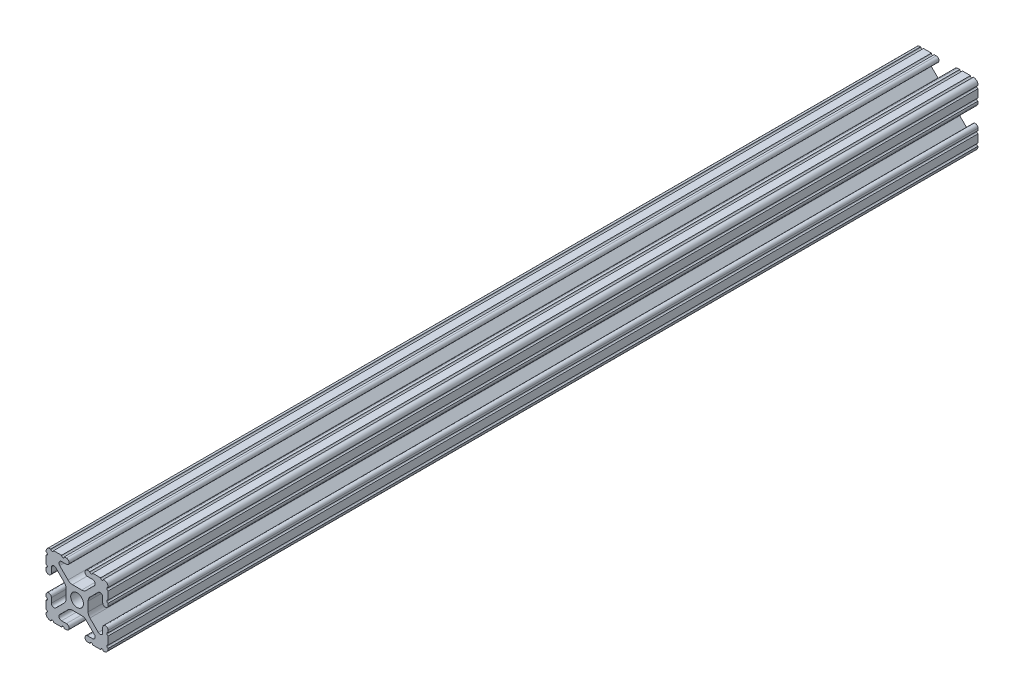
SolidWorks part; units mm, degrees
ref_plane "Front Plane" through (0, 0, 0) normal (0, 0, 1) x (1, 0, 0)
ref_plane "Top Plane" through (0, 0, 0) normal (0, 1, 0) x (1, 0, 0)
ref_plane "Right Plane" through (0, 0, 0) normal (1, 0, 0) x (0, 0, -1)
sketch "Sketch1" plane through (0, 0, 0) normal (0, 0, 1) x (1, 0, 0)
  line L0 (0, -12.7) -> (0, 12.7) construction
  line L1 (12.7, 0) -> (-12.7, 0) construction
  line L2 (3.2512, 12.7) -> (-3.2512, 12.7) construction
  line L3 (0, -4.5212) -> (0, 4.5212) construction
  line L4 (-3.2512, 12.7) -> (-3.2512, 10.4902) construction
  line L5 (12.7, -7.4168) -> (12.7, 7.4168) construction
  line L6 (0, -2.6035) -> (0, 2.6035) construction
  point P4 (0, 0)
  point P8 (0, 0)
  point P11 (0, 12.7)
  point P14 (0, 0)
  point P18 (12.7, 0)
  point P21 (0, 0)
sketch "Sketch2" plane through (0, 0, 0) normal (1, 0, 0) x (0, 0, -1)
  line L0 (-177.8, 0) -> (177.8, 0) construction
  point P4 (0, 0)
  dimension "Length" = 355.6
sketch "Sketch3" plane through (0, 0, 0) normal (0, 0, 1) x (1, 0, 0)
  line L1 (12.7, -12.7) -> (-12.7, -12.7)
  line L2 (12.7, -12.7) -> (12.7, 12.7)
  line L3 (12.7, 12.7) -> (-12.7, 12.7)
  line L4 (-12.7, -12.7) -> (-12.7, 12.7)
  line L5 (12.7, -12.7) -> (-12.7, 12.7) construction
  line L6 (12.7, 12.7) -> (-12.7, -12.7) construction
  point P0 (0, 0)
extrude "Boss-Extrude1" add sketch "Sketch3" along normal up to vertex (177.8 mm away) and the other way up to vertex (177.8 mm away) up to point (0, 0, 177.8) other way up to point (0, 0, -177.8)
sketch "Sketch4" plane through (0, 0, 177.8) normal (0, 0, 1) x (1, 0, 0)
  line L0 (-3.2512, 12.7) -> (-3.2512, 10.4902)
  line L1 (-3.2512, 10.4902) -> (-8.9276, 10.4902)
  line L2 (-8.9276, 10.4902) -> (-2.9586, 4.5212)
  line L3 (-2.9586, 4.5212) -> (2.9586, 4.5212)
  line L4 (0, -12.7) -> (0, 12.7) construction
  line L5 (12.7, 12.7) -> (-12.7, 12.7) construction
  line L6 (0, 12.7) -> (0, -12.7) construction
  line L7 (-12.7, 0) -> (12.7, 0) construction
  line L8 (-12.7, 12.7) -> (0, 0) construction
  line L9 (-12.7, 3.2512) -> (-10.4902, 3.2512)
  line L10 (-10.4902, 3.2512) -> (-10.4902, 8.9276)
  line L11 (-10.4902, 8.9276) -> (-4.5212, 2.9586)
  line L12 (-4.5212, 2.9586) -> (-4.5212, -2.9586)
  line L13 (4.5212, 2.9586) -> (4.5212, -2.9586)
  line L14 (10.4902, 8.9276) -> (4.5212, 2.9586)
  line L15 (10.4902, 3.2512) -> (10.4902, 8.9276)
  line L16 (12.7, 3.2512) -> (10.4902, 3.2512)
  line L17 (8.9276, 10.4902) -> (2.9586, 4.5212)
  line L18 (3.2512, 10.4902) -> (8.9276, 10.4902)
  line L19 (3.2512, 12.7) -> (3.2512, 10.4902)
  line L20 (3.2512, -12.7) -> (3.2512, -10.4902)
  line L21 (3.2512, -10.4902) -> (8.9276, -10.4902)
  line L22 (8.9276, -10.4902) -> (2.9586, -4.5212)
  line L23 (12.7, -3.2512) -> (10.4902, -3.2512)
  line L24 (10.4902, -3.2512) -> (10.4902, -8.9276)
  line L25 (10.4902, -8.9276) -> (4.5212, -2.9586)
  line L26 (-10.4902, -8.9276) -> (-4.5212, -2.9586)
  line L27 (-10.4902, -3.2512) -> (-10.4902, -8.9276)
  line L28 (-12.7, -3.2512) -> (-10.4902, -3.2512)
  line L29 (-2.9586, -4.5212) -> (2.9586, -4.5212)
  line L30 (-8.9276, -10.4902) -> (-2.9586, -4.5212)
  line L31 (-3.2512, -10.4902) -> (-8.9276, -10.4902)
  line L32 (-3.2512, -12.7) -> (-3.2512, -10.4902)
  line L33 (-12.7, 3.2512) -> (-12.7, -3.2512)
  line L34 (-3.2512, -12.7) -> (3.2512, -12.7)
  line L35 (12.7, -3.2512) -> (12.7, 3.2512)
  line L36 (3.2512, 12.7) -> (-3.2512, 12.7)
  line L37 (-12.7, 12.7) -> (-12.7, -12.7) construction
  line L38 (-12.7, -12.7) -> (12.7, -12.7) construction
  arc A3 (-6.3485, 10.4902) -> (-7.1039, 8.6665) centre (-6.3485, 9.4219) ccw
  arc A4 (7.1039, 8.6665) -> (6.3485, 10.4902) centre (6.3485, 9.4219) ccw
  arc A5 (8.6665, -7.1039) -> (10.4902, -6.3485) centre (9.4219, -6.3485) ccw
  arc A6 (10.4902, 6.3485) -> (8.6665, 7.1039) centre (9.4219, 6.3485) ccw
  arc A7 (-7.1039, -8.6665) -> (-6.3485, -10.4902) centre (-6.3485, -9.4219) ccw
  arc A8 (6.3485, -10.4902) -> (7.1039, -8.6665) centre (6.3485, -9.4219) ccw
  arc A9 (-8.6665, 7.1039) -> (-10.4902, 6.3485) centre (-9.4219, 6.3485) ccw
  arc A10 (-10.4902, -6.3485) -> (-8.6665, -7.1039) centre (-9.4219, -6.3485) ccw
  circle A11 centre (0, 0) radius 2.6035
  point P34 (0, 4.5212)
  point P45 (4.5212, 0)
  point P46 (-4.5212, 0)
  point P53 (0, -4.5212)
  point P81 (0, 0)
  line M2 (-12.7, 12.7) -> (-12.7, -12.7)
  line M3 (-12.7, -12.7) -> (12.7, -12.7)
  line M4 (12.7, -12.7) -> (12.7, 12.7)
  line M5 (12.7, 12.7) -> (-12.7, 12.7)
  dimension "D5" = 5.207
  dimension "D1" = 2.2098
  dimension "D2" = 2.2098
  dimension "D3" = 14.8336
  dimension "D4" = 4
extrude "Cut-Extrude1" cut sketch "Sketch4" against normal through all contours L17 A4 L18 L19 L0 L1 A3 L2 L3 M5 | L15 A6 L14 L13 L25 A5 L24 L23 L16 M4 | L21 A8 L22 L29 L30 A7 L31 L32 L20 M3 | L27 A10 L26 L12 L11 A9 L10 L9 L28 M2 | A11
sketch "Sketch5" plane through (0, 0, 177.8) normal (0, 0, 1) x (1, 0, 0)
  line L0 (-4.3561, 12.7) -> (-3.2512, 12.7)
  line L1 (-3.2512, 12.7) -> (-3.2512, 10.4902)
  line L2 (-3.2512, 10.4902) -> (-4.3561, 10.4902)
  line L3 (0, -12.7) -> (0, 12.7) construction
  line L4 (-3.2512, 12.7) -> (-12.7, 12.7) construction
  line L5 (3.2512, 10.4902) -> (4.3561, 10.4902)
  line L6 (3.2512, 12.7) -> (3.2512, 10.4902)
  line L7 (4.3561, 12.7) -> (3.2512, 12.7)
  line L8 (12.7, 4.3561) -> (12.7, 3.2512)
  line L9 (12.7, 3.2512) -> (10.4902, 3.2512)
  line L10 (10.4902, 3.2512) -> (10.4902, 4.3561)
  line L11 (10.4902, -3.2512) -> (10.4902, -4.3561)
  line L12 (12.7, -3.2512) -> (10.4902, -3.2512)
  line L13 (12.7, -4.3561) -> (12.7, -3.2512)
  line L14 (4.3561, -12.7) -> (3.2512, -12.7)
  line L15 (3.2512, -12.7) -> (3.2512, -10.4902)
  line L16 (3.2512, -10.4902) -> (4.3561, -10.4902)
  line L17 (-3.2512, -10.4902) -> (-4.3561, -10.4902)
  line L18 (-3.2512, -12.7) -> (-3.2512, -10.4902)
  line L19 (-4.3561, -12.7) -> (-3.2512, -12.7)
  line L20 (-12.7, -4.3561) -> (-12.7, -3.2512)
  line L21 (-12.7, -3.2512) -> (-10.4902, -3.2512)
  line L22 (-10.4902, -3.2512) -> (-10.4902, -4.3561)
  line L23 (-10.4902, 3.2512) -> (-10.4902, 4.3561)
  line L24 (-12.7, 3.2512) -> (-10.4902, 3.2512)
  line L25 (-12.7, 4.3561) -> (-12.7, 3.2512)
  line L26 (-12.7, 12.7) -> (-12.7, 3.2512) construction
  line L27 (-10.7124, 12.7) -> (-9.6075, 12.7)
  line L28 (-6.3436, 12.7) -> (-5.2387, 12.7)
  line L29 (-12.7, 10.7124) -> (-12.7, 9.6075)
  line L30 (-12.7, 6.3436) -> (-12.7, 5.2387)
  line L31 (6.3437, 12.7) -> (5.2388, 12.7)
  line L32 (10.7125, 12.7) -> (9.6076, 12.7)
  line L33 (12.7, 10.7125) -> (12.7, 9.6075)
  line L34 (12.7, 6.3436) -> (12.7, 5.2387)
  line L35 (12.7, -6.3437) -> (12.7, -5.2388)
  line L36 (12.7, -10.7125) -> (12.7, -9.6076)
  line L37 (10.7125, -12.7) -> (9.6076, -12.7)
  line L38 (6.3437, -12.7) -> (5.2388, -12.7)
  line L39 (-6.3436, -12.7) -> (-5.2387, -12.7)
  line L40 (-10.7124, -12.7) -> (-9.6075, -12.7)
  line L41 (-12.7, -10.7125) -> (-12.7, -9.6076)
  line L42 (-12.7, -6.3437) -> (-12.7, -5.2388)
  line L43 (12.7, 12.7) -> (3.2512, 12.7) construction
  line L44 (12.7, 3.2512) -> (12.7, 12.7) construction
  arc A0 (-4.3561, 10.4902) -> (-4.3561, 12.7) centre (-4.3561, 11.5951) ccw
  arc A1 (4.3561, 10.4902) -> (4.3561, 12.7) centre (4.3561, 11.5951) cw
  arc A2 (10.4902, 4.3561) -> (12.7, 4.3561) centre (11.5951, 4.3561) ccw
  arc A3 (10.4902, -4.3561) -> (12.7, -4.3561) centre (11.5951, -4.3561) cw
  arc A4 (4.3561, -10.4902) -> (4.3561, -12.7) centre (4.3561, -11.5951) ccw
  arc A5 (-4.3561, -10.4902) -> (-4.3561, -12.7) centre (-4.3561, -11.5951) cw
  arc A6 (-10.4902, -4.3561) -> (-12.7, -4.3561) centre (-11.5951, -4.3561) ccw
  arc A7 (-10.4902, 4.3561) -> (-12.7, 4.3561) centre (-11.5951, 4.3561) cw
  arc A8 (-10.7124, 12.7) -> (-9.6075, 12.7) centre (-10.16, 12.7) ccw
  arc A9 (-6.3436, 12.7) -> (-5.2387, 12.7) centre (-5.7912, 12.7) ccw
  arc A10 (-12.7, 9.6075) -> (-12.7, 10.7124) centre (-12.7, 10.16) ccw
  arc A11 (-12.7, 5.2387) -> (-12.7, 6.3436) centre (-12.7, 5.7912) ccw
  arc A12 (5.2388, 12.7) -> (6.3437, 12.7) centre (5.7912, 12.7) ccw
  arc A13 (9.6076, 12.7) -> (10.7125, 12.7) centre (10.16, 12.7) ccw
  arc A14 (12.7, 10.7125) -> (12.7, 9.6075) centre (12.7, 10.16) ccw
  arc A15 (12.7, 6.3436) -> (12.7, 5.2387) centre (12.7, 5.7912) ccw
  arc A16 (12.7, -5.2388) -> (12.7, -6.3437) centre (12.7, -5.7912) ccw
  arc A17 (12.7, -9.6076) -> (12.7, -10.7125) centre (12.7, -10.16) ccw
  arc A18 (10.7125, -12.7) -> (9.6076, -12.7) centre (10.16, -12.7) ccw
  arc A19 (6.3437, -12.7) -> (5.2388, -12.7) centre (5.7912, -12.7) ccw
  arc A20 (-5.2387, -12.7) -> (-6.3436, -12.7) centre (-5.7912, -12.7) ccw
  arc A21 (-9.6075, -12.7) -> (-10.7124, -12.7) centre (-10.16, -12.7) ccw
  arc A22 (-12.7, -10.7125) -> (-12.7, -9.6076) centre (-12.7, -10.16) ccw
  arc A23 (-12.7, -6.3437) -> (-12.7, -5.2388) centre (-12.7, -5.7912) ccw
  point P11 (0, 0)
  point P52 (0, 0)
  point P104 (0, 0)
  line M5 (3.2512, -10.4902) -> (3.2512, -12.7)
  line M6 (3.2512, -12.7) -> (12.7, -12.7)
  line M7 (12.7, -12.7) -> (12.7, -3.2512)
  line M8 (12.7, -3.2512) -> (10.4902, -3.2512)
  line M9 (10.4902, -3.2512) -> (10.4902, -6.3485)
  line M15 (10.4902, 6.3485) -> (10.4902, 3.2512)
  line M16 (10.4902, 3.2512) -> (12.7, 3.2512)
  line M17 (12.7, 3.2512) -> (12.7, 12.7)
  line M18 (12.7, 12.7) -> (3.2512, 12.7)
  line M19 (3.2512, 12.7) -> (3.2512, 10.4902)
  line M20 (3.2512, 10.4902) -> (6.3485, 10.4902)
  line M26 (-6.3485, 10.4902) -> (-3.2512, 10.4902)
  line M27 (-3.2512, 10.4902) -> (-3.2512, 12.7)
  line M28 (-3.2512, 12.7) -> (-12.7, 12.7)
  line M29 (-12.7, 12.7) -> (-12.7, 3.2512)
  line M30 (-12.7, 3.2512) -> (-10.4902, 3.2512)
  line M31 (-10.4902, 3.2512) -> (-10.4902, 6.3485)
  line M37 (-10.4902, -6.3485) -> (-10.4902, -3.2512)
  line M38 (-10.4902, -3.2512) -> (-12.7, -3.2512)
  line M39 (-12.7, -3.2512) -> (-12.7, -12.7)
  line M40 (-12.7, -12.7) -> (-3.2512, -12.7)
  line M41 (-3.2512, -12.7) -> (-3.2512, -10.4902)
  line M42 (-3.2512, -10.4902) -> (-6.3485, -10.4902)
  line M48 (6.3485, -10.4902) -> (3.2512, -10.4902)
  dimension "D2" = 0.5524
  dimension "D3" = 2.54
  dimension "D4" = 2.54
  dimension "D5" = 2.54
  dimension "D6" = 2.54
  dimension "D1" = 4
  dimension "D7" = 4
extrude "Cut-Extrude2" cut sketch "Sketch5" against normal through all contours A7 M30 M29 | A7 L24 M31 | A6 L21 M39 | A6 M37 M38 | A5 L18 M42 | A5 M41 M40 | A4 M48 M5 | A4 L15 M6 | A3 L12 M9 | A3 M8 M7 | A2 M15 M16 | A2 L9 M17 | A1 M19 M18 | A1 L6 M20 | A0 L1 M28 | A0 M26 M27 | A11 L30 | A10 L29 | A8 L27 | A9 L28 | L31 A12 | L32 A13 | L33 A14 | L34 A15 | L42 A23 | L41 A22 | L40 A21 | L39 A20 | L36 A17 | L35 A16 | L37 A18 | L38 A19
fillet "Fillet1" radius 2.54 8 edges at (2.9586, -4.5212, 0) (-2.9586, -4.5212, 0) (4.5212, -2.9586, 0) (4.5212, 2.9586, 0) (-2.9586, 4.5212, 0) (2.9586, 4.5212, 0) (-4.5212, -2.9586, 0) (-4.5212, 2.9586, 0)
fillet "Fillet2" radius 1.778 4 edges at (12.7, -12.7, 0) (12.7, 12.7, 0) (-12.7, -12.7, 0) (-12.7, 12.7, 0)
equation "\"D2@Sketch4\"=\"Thickness@Sketch1\""
equation "\"D1@Sketch4\"=\"Thickness@Sketch1\""
equation "\"D3@Sketch4\"=\"Opening Width@Sketch1\""
equation "\"D5@Sketch4\"=\"Hole Dia@Sketch1\""
equation "\"D2@Sketch5\"=\"Thickness@Sketch1\"/4"
equation "\"D3@Sketch5\"=\"Height@Sketch1\"/10"
equation "\"D4@Sketch5\"=\"D3@Sketch5\""
equation "\"D5@Sketch5\"=\"D4@Sketch5\""
equation "\"D6@Sketch5\"=\"D5@Sketch5\""
